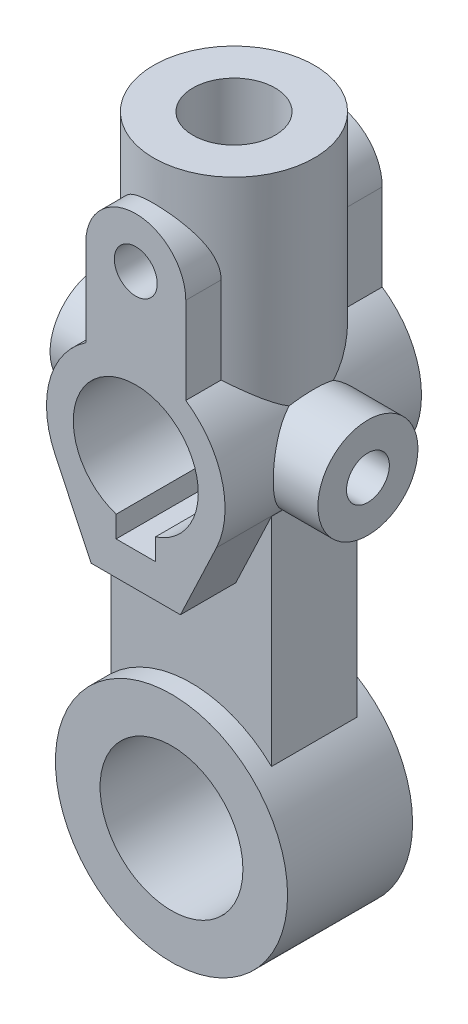
SolidWorks part; units mm, degrees
ref_plane "Alzado" through (0, 0, 0) normal (0, 0, 1) x (1, 0, 0)
ref_plane "Planta" through (0, 0, 0) normal (0, 1, 0) x (1, 0, 0)
ref_plane "Vista lateral" through (0, 0, 0) normal (1, 0, 0) x (0, 0, -1)
sketch "Croquis1" plane through (0, 0, 0) normal (0, 0, 1) x (1, 0, 0)
  line L0 (0, 0) -> (0, 45) construction
  line L1 (14, 20.7123) -> (14, 45)
  line L2 (-14, 20.7123) -> (-14, 45)
  line L3 (-12.5, -32) -> (12.5, -32)
  line L4 (12.5, -32) -> (22.5914, -10.7065)
  line L5 (-12.5, -32) -> (-22.5914, -10.7065)
  line L6 (0, 0) -> (0, -32) construction
  line L7 (0, 0) -> (0, -22.6132) construction
  arc A0 (22.5914, -10.7065) -> (14, 20.7123) centre (0, 0) ccw
  arc A1 (-14, 45) -> (14, 45) centre (0, 45) cw
  arc A2 (-14, 20.7123) -> (-22.5914, -10.7065) centre (0, 0) ccw
  dimension "D1" = 14
  dimension "D2" = 45
  dimension "D3" = 50
  dimension "D4" = 32
  dimension "D5" = 25
extrude "Saliente-Extruir3" add sketch "Croquis1" along normal mid plane 55
sketch "Croquis3" plane through (0, 0, 0) normal (0, 1, 0) x (1, 0, 0)
  circle A0 centre (0, 0) radius 22.5
  dimension "D1" = 45
extrude "Saliente-Extruir4" add sketch "Croquis3" along normal blind 70
sketch "Croquis4" plane through (0, 0, 0) normal (0, 1, 0) x (1, 0, 0)
  line L0 (-22.5, 12) -> (22.5, -12) construction
  line L4 (-22.5, -12) -> (22.5, -12)
  line L5 (22.5, 12) -> (22.5, -12)
  line L6 (-22.5, 12) -> (22.5, 12)
  line L7 (-22.5, 12) -> (-22.5, -12)
  dimension "D1" = 45
  dimension "D2" = 24
extrude "Saliente-Extruir5" add sketch "Croquis4" against normal blind 95
sketch "Croquis5" plane through (0, 0, 0) normal (0, 0, 1) x (1, 0, 0)
  line L0 (-22.5, -95) -> (22.5, -95) construction
  circle A1 centre (0, -95) radius 32.5
  dimension "D1" = 65
extrude "Saliente-Extruir6" add sketch "Croquis5" along normal mid plane 35
sketch "Croquis6" plane through (0, 0, 0) normal (1, 0, 0) x (0, 0, -1)
  circle A0 centre (0, 0) radius 14
  dimension "D1" = 28
extrude "Saliente-Extruir7" add sketch "Croquis6" along normal mid plane 75
sketch "Croquis7" plane through (0, 0, 0) normal (0, 0, 1) x (1, 0, 0)
  line L0 (0, 0) -> (0, 17.5) construction
  line L1 (0, 17.5) -> (0, 45) construction
  line L3 (5.5, -22.6132) -> (5.5, -16.6132)
  line L4 (-5.5, -22.6132) -> (5.5, -22.6132)
  line L5 (-5.5, -22.6132) -> (-5.5, -16.6132)
  line L6 (0, -22.6132) -> (0, 0) construction
  circle A2 centre (0, 45) radius 6
  arc A3 (5.5, -16.6132) -> (-5.5, -16.6132) centre (0, 0) ccw
  dimension "D1" = 12
  dimension "D2" = 45
  dimension "D3" = 17.5
  dimension "D4" = 6
  dimension "D5" = 11
extrude "Cortar-Extruir1" cut sketch "Croquis7" against normal through all both and the other way through all
sketch "Croquis8" plane through (37.5, 0, 0) normal (1, 0, 0) x (0, 0, -1)
  circle A1 centre (0, 0) radius 6
  dimension "D1" = 12
extrude "Cortar-Extruir2" cut sketch "Croquis8" against normal through all
sketch "Croquis9" plane through (0, 0, 17.5) normal (0, 0, 1) x (1, 0, 0)
  circle A1 centre (0, -95) radius 20
  dimension "D1" = 40
extrude "Cortar-Extruir3" cut sketch "Croquis9" against normal through all
sketch "Croquis10" plane through (0, 70, 0) normal (0, 1, 0) x (1, 0, 0)
  circle A1 centre (0, 0) radius 11.5
  dimension "D1" = 23
extrude "Cortar-Extruir4" cut sketch "Croquis10" against normal up to next
